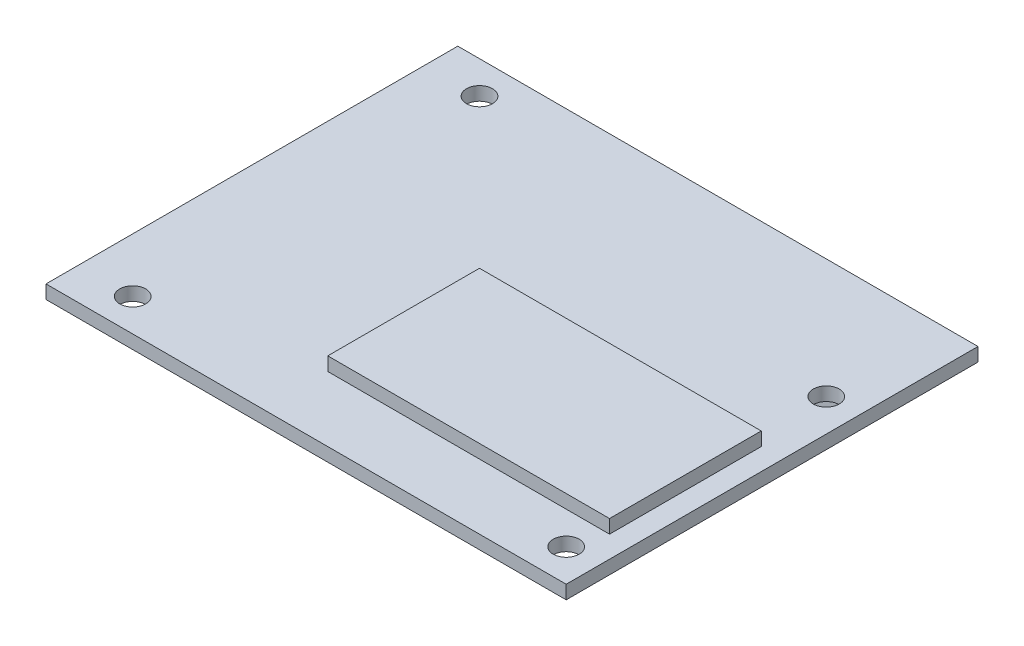
SolidWorks part; units mm, degrees
ref_plane "Front Plane" through (0, 0, 0) normal (0, 0, 1) x (1, 0, 0)
ref_plane "Top Plane" through (0, 0, 0) normal (0, 1, 0) x (1, 0, 0)
ref_plane "Right Plane" through (0, 0, 0) normal (1, 0, 0) x (0, 0, -1)
sketch "Sketch1" plane through (0, 0, 0) normal (0, 1, 0) x (1, 0, 0)
  line L1 (-29.4724, 18.6705) -> (31.4876, 18.6705)
  line L2 (-29.4724, 18.6705) -> (-29.4724, -29.5895)
  line L3 (-29.4724, -29.5895) -> (31.4876, -29.5895)
  line L4 (31.4876, 18.6705) -> (31.4876, -29.5895)
  dimension "D1" = 60.96
  dimension "D2" = 48.26
extrude "Boss-Extrude1" add sketch "Sketch1" along normal blind 1.5875
sketch "Sketch2" plane through (0, 1.5875, 0) normal (0, 1, 0) x (1, 0, 0)
  line L1 (-4.0724, -4.1895) -> (28.9476, -4.1895)
  line L2 (-4.0724, -4.1895) -> (-4.0724, -21.9695)
  line L3 (-4.0724, -21.9695) -> (28.9476, -21.9695)
  line L4 (28.9476, -4.1895) -> (28.9476, -21.9695)
  line L6 (31.4876, -29.5895) -> (31.4876, 18.6705) construction
  line L7 (-29.4724, -29.5895) -> (31.4876, -29.5895) construction
  dimension "D1" = 17.78
  dimension "D2" = 33.02
  dimension "D3" = 2.54
  dimension "D4" = 7.62
extrude "Boss-Extrude2" add sketch "Sketch2" along normal blind 1.5875
sketch "Sketch3" plane through (0, 1.5875, 0) normal (0, 1, 0) x (1, 0, 0)
  line L0 (-29.4724, -29.5895) -> (31.4876, -29.5895) construction
  line L1 (-29.4724, 18.6705) -> (-29.4724, -29.5895) construction
  line L2 (31.4876, -29.5895) -> (31.4876, 18.6705) construction
  line L3 (31.4876, 18.6705) -> (-29.4724, 18.6705) construction
  circle A0 centre (-23.1224, 14.8605) radius 1.524
  circle A1 centre (27.6776, 4.7005) radius 1.524
  circle A2 centre (-23.1224, -25.7795) radius 1.524
  circle A3 centre (27.6776, -25.7795) radius 1.524
  point P8 (0, 0)
  dimension "D1" = 3.048
  dimension "D2" = 3.81
  dimension "D3" = 6.35
  dimension "D4" = 3.81
  dimension "D5" = 3.81
  dimension "D6" = 13.97
extrude "Cut-Extrude1" cut sketch "Sketch3" against normal through all
sketch "Sketch4" plane through (0, 0, 0) normal (0, -1, 0) x (-1, 0, 0)
  line L1 (-8.6276, 13.5905) -> (-21.3276, 13.5905)
  line L2 (-8.6276, 13.5905) -> (-8.6276, 16.1305)
  line L3 (-8.6276, 16.1305) -> (-21.3276, 16.1305)
  line L4 (-21.3276, 13.5905) -> (-21.3276, 16.1305)
  line L6 (-31.4876, -29.5895) -> (-31.4876, 18.6705) construction
  line L7 (-31.4876, 18.6705) -> (29.4724, 18.6705) construction
  dimension "D1" = 2.54
  dimension "D2" = 12.7
  dimension "D3" = 10.16
  dimension "D4" = 2.54
extrude "Boss-Extrude3" add sketch "Sketch4" along normal blind 10.16
